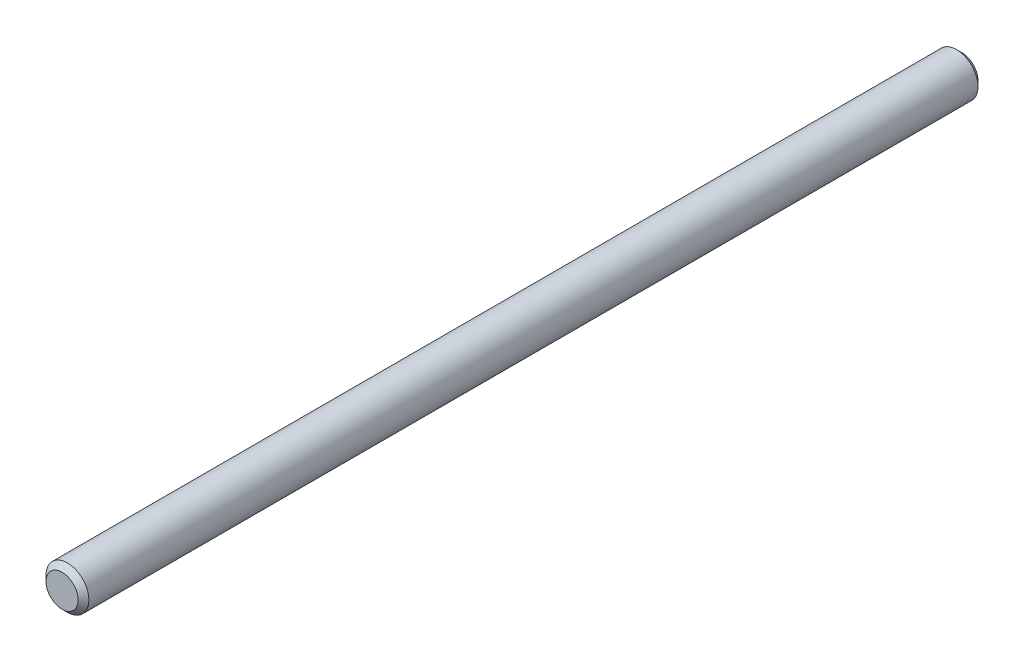
SolidWorks part; units mm, degrees
ref_plane "Front Plane" through (0, 0, 0) normal (0, 0, 1) x (1, 0, 0)
ref_plane "Top Plane" through (0, 0, 0) normal (0, 1, 0) x (1, 0, 0)
ref_plane "Right Plane" through (0, 0, 0) normal (1, 0, 0) x (0, 0, -1)
sketch "Sketch1" plane through (0, 0, 0) normal (0, 0, 1) x (1, 0, 0)
  circle A0 centre (0, 0) radius 2
  dimension "D1" = 4
extrude "Boss-Extrude1" add sketch "Sketch1" along normal mid plane 84
cosmetic thread "Cosmetic Thread1" parameters "D1"=8, "D2"=3.22
cosmetic thread "Cosmetic Thread2" parameters "D1"=12, "D2"=3.22
chamfer "Chamfer1" distance 0.5 angle 45 2 edges at (2, 0, 42) (2, 0, -42)
